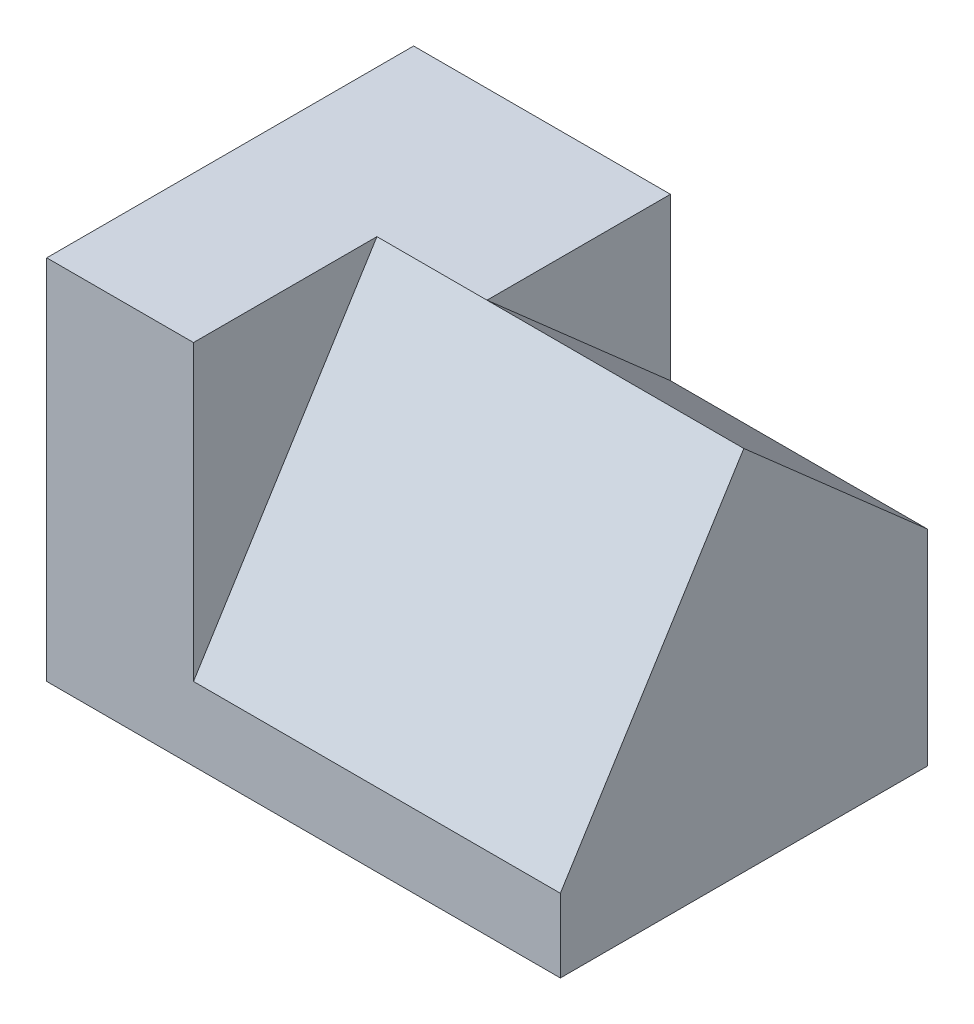
SolidWorks part; units mm, degrees
ref_plane "Front Plane" through (0, 0, 0) normal (0, 0, 1) x (1, 0, 0)
ref_plane "Top Plane" through (0, 0, 0) normal (0, 1, 0) x (1, 0, 0)
ref_plane "Right Plane" through (0, 0, 0) normal (1, 0, 0) x (0, 0, -1)
sketch "Sketch1" plane through (0, 0, 0) normal (0, 1, 0) x (1, 0, 0)
  line L1 (-35, 25) -> (35, 25)
  line L2 (-35, 25) -> (-35, -25)
  line L3 (-35, -25) -> (35, -25)
  line L4 (35, 25) -> (35, -25)
  line L5 (-35, 25) -> (35, -25) construction
  line L6 (-35, -25) -> (35, 25) construction
  point P0 (0, 0)
  dimension "D1" = 70
  dimension "D2" = 50
extrude "Boss-Extrude1" add sketch "Sketch1" along normal blind 10
sketch "Sketch2" plane through (0, 10, 0) normal (0, 1, 0) x (1, 0, 0)
  line L0 (-35, -25) -> (-15, -25)
  line L1 (-35, -25) -> (35, -25) construction
  line L2 (-15, -25) -> (-15, 0)
  line L4 (0, 0) -> (0, 25)
  line L5 (35, 25) -> (-35, 25) construction
  line L6 (35, -25) -> (35, 25) construction
  line L7 (0, 25) -> (-35, 25)
  line L8 (-35, 25) -> (-35, -25)
  line L9 (-15, 0) -> (0, 0)
  line L11 (35, -25) -> (35, 25)
  line L12 (35, 25) -> (-35, 25)
  line L13 (-35, 25) -> (-35, -25)
  line L14 (-35, -25) -> (35, -25)
  line L15 (35, -25) -> (35, 25)
  line L16 (35, 25) -> (0, 25)
  line L18 (-35, -25) -> (35, -25)
  dimension "D1" = 20
  dimension "D2" = 25
  dimension "D3" = 35
  dimension "D4" = 0
sketch "Sketch3" plane through (0, 10, 0) normal (0, 1, 0) x (1, 0, 0)
  line L0 (-35, 25) -> (0, 25)
  line L1 (0, 25) -> (0, 0)
  line L2 (0, 0) -> (-15, 0)
  line L3 (-15, 0) -> (-15, -25)
  line L4 (-15, -25) -> (-35, -25)
  line L5 (-35, -25) -> (-35, 25)
extrude "Boss-Extrude2" add sketch "Sketch3" along normal blind 40
sketch "Sketch4" plane through (35, 0, 0) normal (1, 0, 0) x (0, 0, -1)
  line L1 (25, 10) -> (25, 28)
  line L2 (25, 50) -> (25, 10) construction
  line L3 (25, 28) -> (0, 50)
  line L4 (0, 50) -> (-25, 10)
  line L5 (-25, 10) -> (25, 10)
  dimension "D1" = 18
extrude "Boss-Extrude3" add sketch "Sketch4" against normal blind 50
